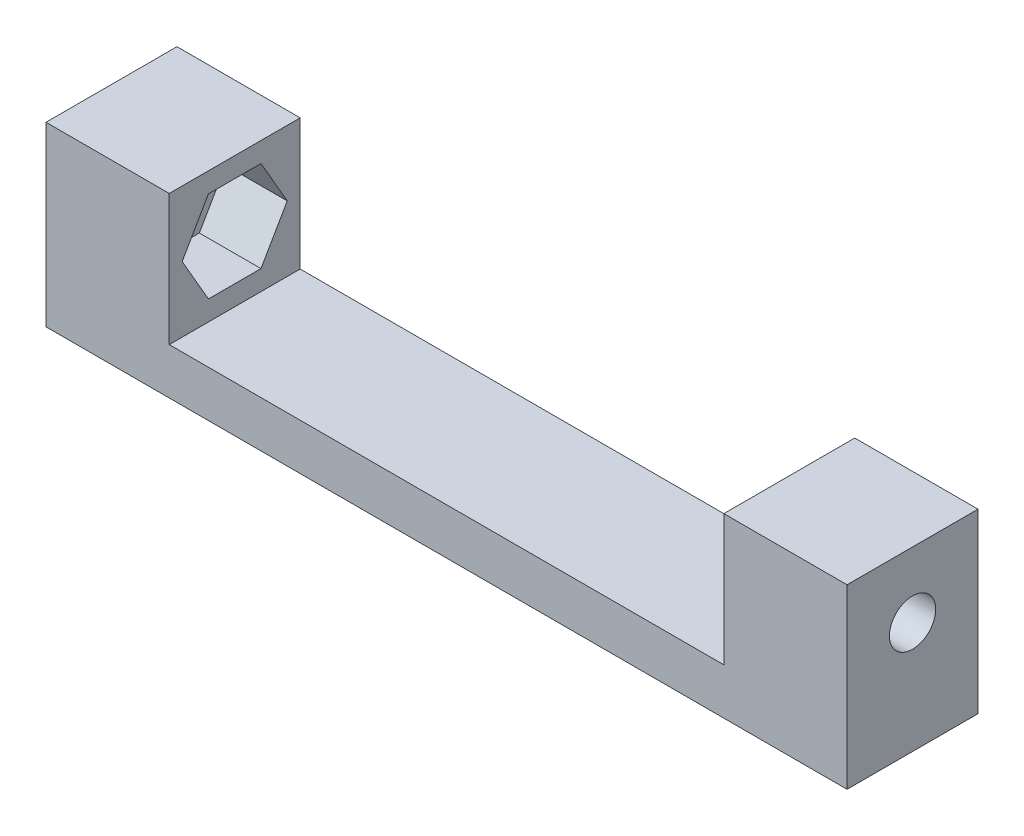
SolidWorks part; units mm, degrees
ref_plane "Front Plane" through (0, 0, 0) normal (0, 0, 1) x (1, 0, 0)
ref_plane "Top Plane" through (0, 0, 0) normal (0, 1, 0) x (1, 0, 0)
ref_plane "Right Plane" through (0, 0, 0) normal (1, 0, 0) x (0, 0, -1)
sketch "Sketch1" plane through (0, 0, 0) normal (1, 0, 0) x (0, 0, -1)
  line L0 (0, 0) -> (1.6017, 0) construction
  line L1 (1.705, 2.9531) -> (-1.705, 2.9531)
  line L2 (-1.705, 2.9531) -> (-3.41, 0)
  line L3 (-3.41, 0) -> (-1.705, -2.9531)
  line L4 (-1.705, -2.9531) -> (1.705, -2.9531)
  line L5 (1.705, -2.9531) -> (3.41, 0)
  line L6 (3.41, 0) -> (1.705, 2.9531)
  line L8 (-4.25, -4.25) -> (4.25, -4.25)
  line L9 (-4.25, -4.25) -> (-4.25, 4.25)
  line L10 (-4.25, 4.25) -> (4.25, 4.25)
  line L11 (4.25, -4.25) -> (4.25, 4.25)
  line L12 (-4.25, -4.25) -> (4.25, 4.25) construction
  line L13 (-4.25, 4.25) -> (4.25, -4.25) construction
  circle A0 centre (0, 0) radius 2.9531 construction
  dimension "D1" = 3.41
  dimension "D2" = 8.5
  dimension "D3" = 8.5
extrude "Boss-Extrude1" add sketch "Sketch1" along normal blind 5
sketch "Sketch2" plane through (0, 0, 0) normal (-1, 0, 0) x (0, 0, 1)
  line L1 (-4.25, -4.25) -> (4.25, -4.25)
  line L2 (-4.25, -4.25) -> (-4.25, 4.25)
  line L3 (-4.25, 4.25) -> (4.25, 4.25)
  line L4 (4.25, -4.25) -> (4.25, 4.25)
  line L5 (-4.25, -4.25) -> (4.25, 4.25) construction
  line L6 (-4.25, 4.25) -> (4.25, -4.25) construction
  point P0 (0, 0)
extrude "Boss-Extrude2" add sketch "Sketch2" along normal blind 2
sketch "Sketch3" plane through (0, 0, 0) normal (1, 0, 0) x (0, 0, -1)
  circle A0 centre (0, 0) radius 1.5
  dimension "D1" = 3
extrude "Cut-Extrude1" cut sketch "Sketch3" against normal blind 2
sketch "Sketch4" plane through (0, -4.25, 0) normal (0, -1, 0) x (1, 0, 0)
  line L0 (5, -4.25) -> (-2, -4.25) construction
  line L1 (-2, 4.25) -> (50, 4.25)
  line L2 (-2, 4.25) -> (-2, -4.25)
  line L3 (-2, -4.25) -> (50, -4.25)
  line L4 (50, 4.25) -> (50, -4.25)
  dimension "D1" = 52
extrude "Boss-Extrude3" add sketch "Sketch4" along normal blind 3
sketch "Sketch5" plane through (0, -4.25, 0) normal (0, 1, 0) x (1, 0, 0)
  line L0 (50, -4.25) -> (5, -4.25) construction
  line L1 (50, 4.25) -> (43, 4.25)
  line L2 (50, 4.25) -> (50, -4.25)
  line L3 (50, -4.25) -> (43, -4.25)
  line L4 (43, 4.25) -> (43, -4.25)
  dimension "D1" = 7
extrude "Boss-Extrude4" add sketch "Sketch5" along normal up to surface (8.5 mm away) up to face at (1.5, 4.25, 0)
sketch "Sketch6" plane through (43, 0, 0) normal (-1, 0, 0) x (0, 0, 1)
  line L0 (-4.25, -4.25) -> (4.25, -4.25) construction
  line L1 (3.41, 0) -> (1.705, 2.9531)
  line L2 (1.705, 2.9531) -> (-1.705, 2.9531)
  line L3 (-1.705, 2.9531) -> (-3.41, 0)
  line L4 (-3.41, 0) -> (-1.705, -2.9531)
  line L5 (-1.705, -2.9531) -> (1.705, -2.9531)
  line L6 (1.705, -2.9531) -> (3.41, 0)
  circle A0 centre (0, 0) radius 2.9531 construction
  dimension "D1" = 3.41
extrude "Cut-Extrude2" cut sketch "Sketch6" against normal blind 5
sketch "Sketch7" plane through (48, 0, 0) normal (-1, 0, 0) x (0, 0, 1)
  circle A0 centre (0, 0) radius 1.5
  dimension "D1" = 3
extrude "Cut-Extrude3" cut sketch "Sketch7" against normal blind 5
sketch "Sketch8" plane through (0, 0, 0) normal (1, 0, 0) x (0, 0, -1)
  line L0 (-1.705, 2.9531) -> (-3.41, 0) construction
  line L1 (-3.41, 0) -> (-1.705, -2.9531) construction
  line L2 (-1.705, -2.9531) -> (1.705, -2.9531) construction
  line L3 (1.705, -2.9531) -> (3.41, 0) construction
  line L4 (3.41, 0) -> (1.705, 2.9531) construction
  line L5 (1.705, 2.9531) -> (-1.705, 2.9531) construction
  line L6 (-1.705, 2.9531) -> (-3.41, 0)
  line L7 (-3.41, 0) -> (-1.705, -2.9531)
  line L8 (-1.705, -2.9531) -> (1.705, -2.9531)
  line L9 (1.705, -2.9531) -> (3.41, 0)
  line L10 (3.41, 0) -> (1.705, 2.9531)
  line L11 (1.705, 2.9531) -> (-1.705, 2.9531)
  circle A0 centre (0, 0) radius 1.5 construction
  circle A1 centre (0, 0) radius 1.5
extrude "Boss-Extrude5" add sketch "Sketch8" along normal blind 2.5
sketch "Sketch9" plane through (48, 0, 0) normal (-1, 0, 0) x (0, 0, 1)
  line L0 (3.41, 0) -> (1.705, 2.9531) construction
  line L1 (1.705, -2.9531) -> (3.41, 0) construction
  line L2 (-1.705, -2.9531) -> (1.705, -2.9531) construction
  line L3 (-3.41, 0) -> (-1.705, -2.9531) construction
  line L4 (1.705, 2.9531) -> (-1.705, 2.9531) construction
  line L5 (-1.705, 2.9531) -> (-3.41, 0) construction
  line L6 (3.41, 0) -> (1.705, 2.9531)
  line L7 (1.705, -2.9531) -> (3.41, 0)
  line L8 (-1.705, -2.9531) -> (1.705, -2.9531)
  line L9 (-3.41, 0) -> (-1.705, -2.9531)
  line L10 (1.705, 2.9531) -> (-1.705, 2.9531)
  line L11 (-1.705, 2.9531) -> (-3.41, 0)
  circle A0 centre (0, 0) radius 1.5 construction
  circle A1 centre (0, 0) radius 1.5
extrude "Boss-Extrude6" add sketch "Sketch9" along normal blind 2.5
sketch "Sketch10" plane through (5, 0, 0) normal (1, 0, 0) x (0, 0, -1)
  line L0 (3.41, 0) -> (1.705, 2.9531) construction
  line L1 (1.705, -2.9531) -> (3.41, 0) construction
  line L2 (-1.705, -2.9531) -> (1.705, -2.9531) construction
  line L3 (-3.41, 0) -> (-1.705, -2.9531) construction
  line L4 (-1.705, 2.9531) -> (-3.41, 0) construction
  line L5 (1.705, 2.9531) -> (-1.705, 2.9531) construction
  line L6 (3.41, 0) -> (1.705, 2.9531)
  line L7 (1.705, -2.9531) -> (3.41, 0)
  line L8 (-1.705, -2.9531) -> (1.705, -2.9531)
  line L9 (-3.41, 0) -> (-1.705, -2.9531)
  line L10 (-1.705, 2.9531) -> (-3.41, 0)
  line L11 (1.705, 2.9531) -> (-1.705, 2.9531)
  line L13 (-4.25, 4.25) -> (4.25, 4.25)
  line L14 (-4.25, 4.25) -> (-4.25, -4.25)
  line L15 (-4.25, -4.25) -> (4.25, -4.25)
  line L16 (4.25, 4.25) -> (4.25, -4.25)
extrude "Boss-Extrude7" add sketch "Sketch10" along normal blind 1
sketch "Sketch11" plane through (43, 0, 0) normal (-1, 0, 0) x (0, 0, 1)
  line L0 (-3.41, 0) -> (-1.705, -2.9531) construction
  line L1 (-1.705, -2.9531) -> (1.705, -2.9531) construction
  line L2 (1.705, -2.9531) -> (3.41, 0) construction
  line L3 (3.41, 0) -> (1.705, 2.9531) construction
  line L4 (1.705, 2.9531) -> (-1.705, 2.9531) construction
  line L5 (-1.705, 2.9531) -> (-3.41, 0) construction
  line L6 (-3.41, 0) -> (-1.705, -2.9531)
  line L7 (-1.705, -2.9531) -> (1.705, -2.9531)
  line L8 (1.705, -2.9531) -> (3.41, 0)
  line L9 (3.41, 0) -> (1.705, 2.9531)
  line L10 (1.705, 2.9531) -> (-1.705, 2.9531)
  line L11 (-1.705, 2.9531) -> (-3.41, 0)
  line L13 (-4.25, 4.25) -> (4.25, 4.25)
  line L14 (-4.25, 4.25) -> (-4.25, -4.25)
  line L15 (-4.25, -4.25) -> (4.25, -4.25)
  line L16 (4.25, 4.25) -> (4.25, -4.25)
extrude "Boss-Extrude8" add sketch "Sketch11" along normal blind 1
sketch "Sketch12" plane through (2.5, 0, 0) normal (1, 0, 0) x (0, 0, -1)
  line L0 (1.705, -2.9531) -> (3.41, 0) construction
  line L1 (3.41, 0) -> (1.705, 2.9531) construction
  line L2 (-1.705, -2.9531) -> (1.705, -2.9531) construction
  line L3 (1.705, 2.9531) -> (-1.705, 2.9531) construction
  line L4 (-3.41, 0) -> (-1.705, -2.9531) construction
  line L5 (-1.705, 2.9531) -> (-3.41, 0) construction
  line L6 (1.705, -2.9531) -> (3.41, 0)
  line L7 (3.41, 0) -> (1.705, 2.9531)
  line L8 (-1.705, -2.9531) -> (1.705, -2.9531)
  line L9 (1.705, 2.9531) -> (-1.705, 2.9531)
  line L10 (-3.41, 0) -> (-1.705, -2.9531)
  line L11 (-1.705, 2.9531) -> (-3.41, 0)
extrude "Cut-Extrude4" cut sketch "Sketch12" against normal blind 0.5
sketch "Sketch13" plane through (45.5, 0, 0) normal (-1, 0, 0) x (0, 0, 1)
  line L0 (1.705, 2.9531) -> (-1.705, 2.9531) construction
  line L1 (-1.705, 2.9531) -> (-3.41, 0) construction
  line L2 (-3.41, 0) -> (-1.705, -2.9531) construction
  line L3 (-1.705, -2.9531) -> (1.705, -2.9531) construction
  line L4 (1.705, -2.9531) -> (3.41, 0) construction
  line L5 (3.41, 0) -> (1.705, 2.9531) construction
  line L6 (1.705, 2.9531) -> (-1.705, 2.9531)
  line L7 (-1.705, 2.9531) -> (-3.41, 0)
  line L8 (-3.41, 0) -> (-1.705, -2.9531)
  line L9 (-1.705, -2.9531) -> (1.705, -2.9531)
  line L10 (1.705, -2.9531) -> (3.41, 0)
  line L11 (3.41, 0) -> (1.705, 2.9531)
extrude "Cut-Extrude5" cut sketch "Sketch13" against normal blind 0.5
